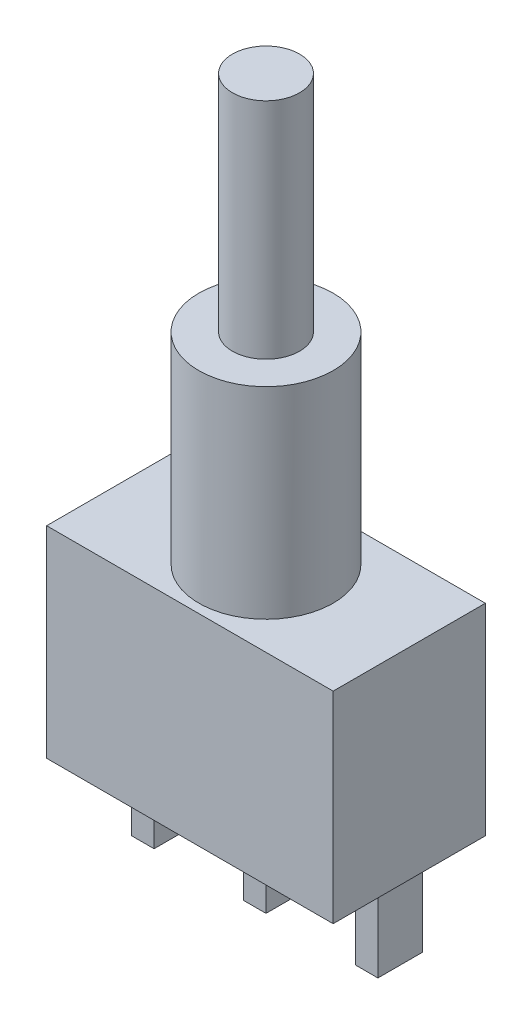
SolidWorks part; units mm, degrees
ref_plane "Plan de face" through (0, 0, 0) normal (0, 0, 1) x (1, 0, 0)
ref_plane "Plan de dessus" through (0, 0, 0) normal (0, 1, 0) x (1, 0, 0)
ref_plane "Plan de droite" through (0, 0, 0) normal (1, 0, 0) x (0, 0, -1)
sketch "Esquisse1" plane through (0, 0, 0) normal (0, 0, 1) x (1, 0, 0)
  line L1 (0, 0) -> (12.8, 0)
  line L2 (0, 0) -> (0, 9)
  line L3 (0, 9) -> (12.8, 9)
  line L4 (12.8, 0) -> (12.8, 9)
  dimension "D1" = 12.8
  dimension "D2" = 9
extrude "Boss.-Extru.1" add sketch "Esquisse1" along normal blind 6.8
sketch "Esquisse2" plane through (0, 0, 0) normal (0, -1, 0) x (1, 0, 0)
  line L0 (0, 6.8) -> (12.8, 6.8) construction
  line L1 (0.9, 1.9) -> (1.9, 1.9)
  line L2 (0.9, 1.9) -> (0.9, 3.9)
  line L3 (0.9, 3.9) -> (1.9, 3.9)
  line L4 (1.9, 1.9) -> (1.9, 3.9)
  line L6 (5.9, 1.9) -> (5.9, 3.9)
  line L7 (5.9, 3.9) -> (6.9, 3.9)
  line L8 (6.9, 1.9) -> (6.9, 3.9)
  line L9 (5.9, 1.9) -> (6.9, 1.9)
  line L10 (10.9, 1.9) -> (10.9, 3.9)
  line L11 (10.9, 3.9) -> (11.9, 3.9)
  line L12 (11.9, 1.9) -> (11.9, 3.9)
  line L13 (10.9, 1.9) -> (11.9, 1.9)
  line L14 (0, 6.8) -> (0, 0) construction
  dimension "D1" = 1
  dimension "D2" = 2
  dimension "D3" = 2.9
  dimension "D4" = 3
  dimension "D5" = 4
  dimension "D6" = 4
  dimension "D7" = 0.9
extrude "Boss.-Extru.2" add sketch "Esquisse2" along normal blind 4
sketch "Esquisse3" plane through (0, 9, 0) normal (0, 1, 0) x (1, 0, 0)
  line L2 (12.8, -6.8) -> (0, -6.8) construction
  line L4 (12.8, -6.8) -> (12.8, 0) construction
  circle A0 centre (6.4, -3.4) radius 3
  dimension "D1" = 6
  dimension "D2" = 3.4
  dimension "D3" = 6.4
extrude "Boss.-Extru.3" add sketch "Esquisse3" along normal blind 9
sketch "Esquisse4" plane through (0, 18, 0) normal (0, 1, 0) x (1, 0, 0)
  circle A0 centre (6.4, -3.4) radius 1.5
  dimension "3" = 3
extrude "Boss.-Extru.4" add sketch "Esquisse4" along normal blind 10
